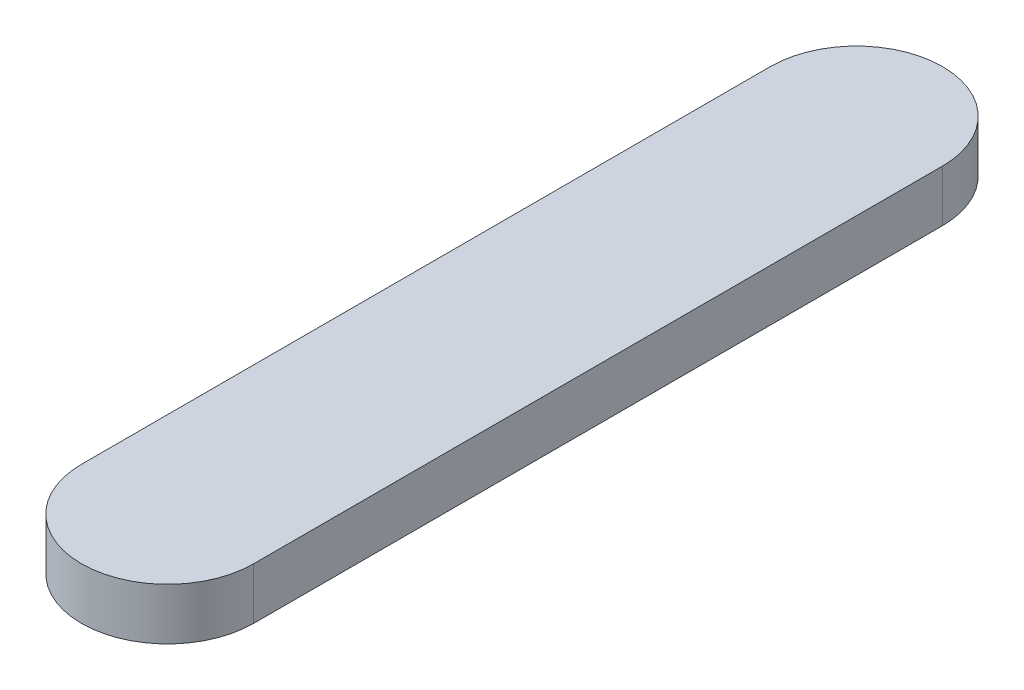
SolidWorks part; units mm, degrees
ref_plane "前视基准面" through (0, 0, 0) normal (0, 0, 1) x (1, 0, 0)
ref_plane "上视基准面" through (0, 0, 0) normal (0, 1, 0) x (1, 0, 0)
ref_plane "右视基准面" through (0, 0, 0) normal (1, 0, 0) x (0, 0, -1)
sketch "草图1" plane through (0, 0, 0) normal (0, 1, 0) x (1, 0, 0)
  line L0 (0, 200) -> (0, -200) construction
  line L1 (50, 200) -> (50, -200)
  line L2 (-50, 200) -> (-50, -200)
  arc A0 (50, 200) -> (-50, 200) centre (0, 200) ccw
  arc A1 (-50, -200) -> (50, -200) centre (0, -200) ccw
  point P2 (0, 0)
  dimension "D1" = 400
  dimension "D2" = 100
extrude "凸台-拉伸1" add sketch "草图1" along normal blind 30
